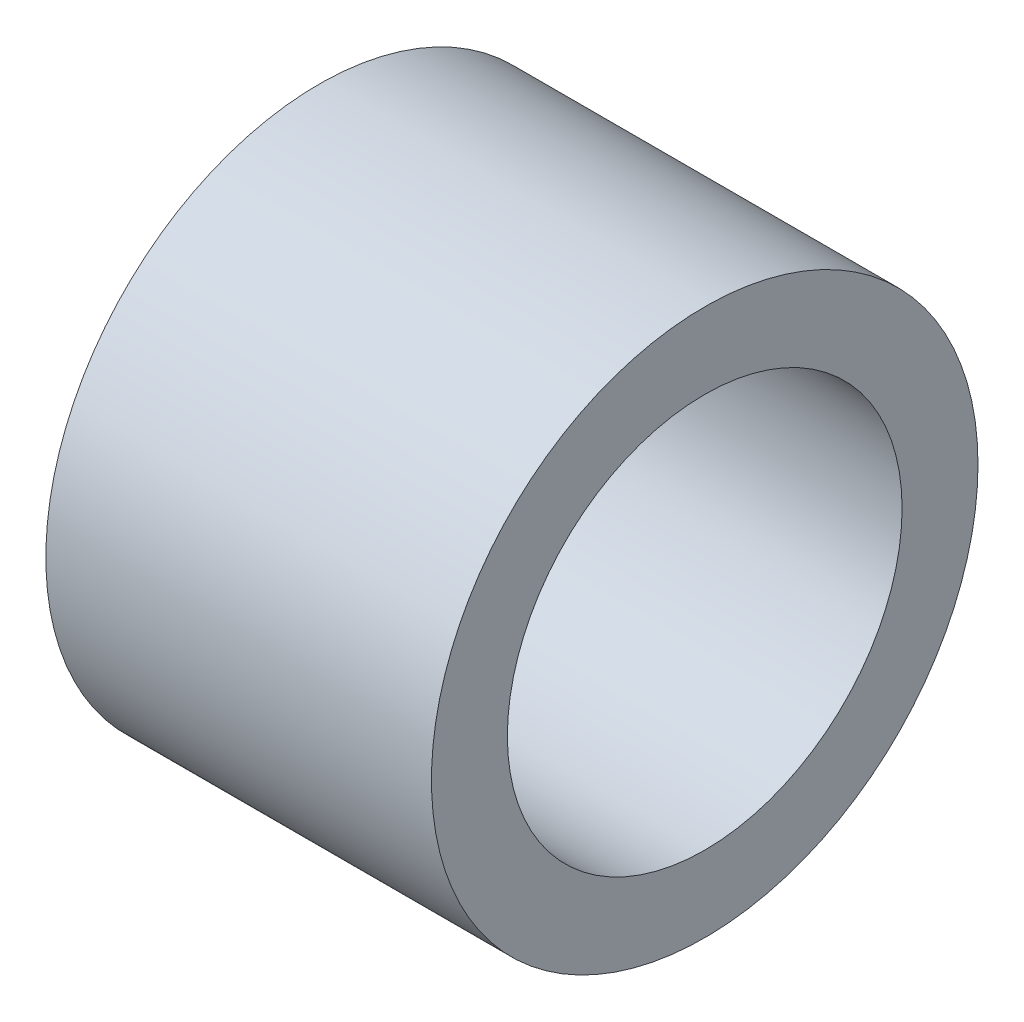
SolidWorks part; units mm, degrees
material "Rubber"
ref_plane "Front Plane" through (0, 0, 0) normal (0, 0, 1) x (1, 0, 0)
ref_plane "Top Plane" through (0, 0, 0) normal (0, 1, 0) x (1, 0, 0)
ref_plane "Right Plane" through (0, 0, 0) normal (1, 0, 0) x (0, 0, -1)
sketch "Sketch1" plane through (0, 0, 0) normal (1, 0, 0) x (0, 0, -1)
  circle A0 centre (0, 0) radius 9
  circle A1 centre (0, 0) radius 6.5
  dimension "D1" = 18
  dimension "D2" = 13
extrude "Boss-Extrude1" add sketch "Sketch1" along normal blind 12.7
